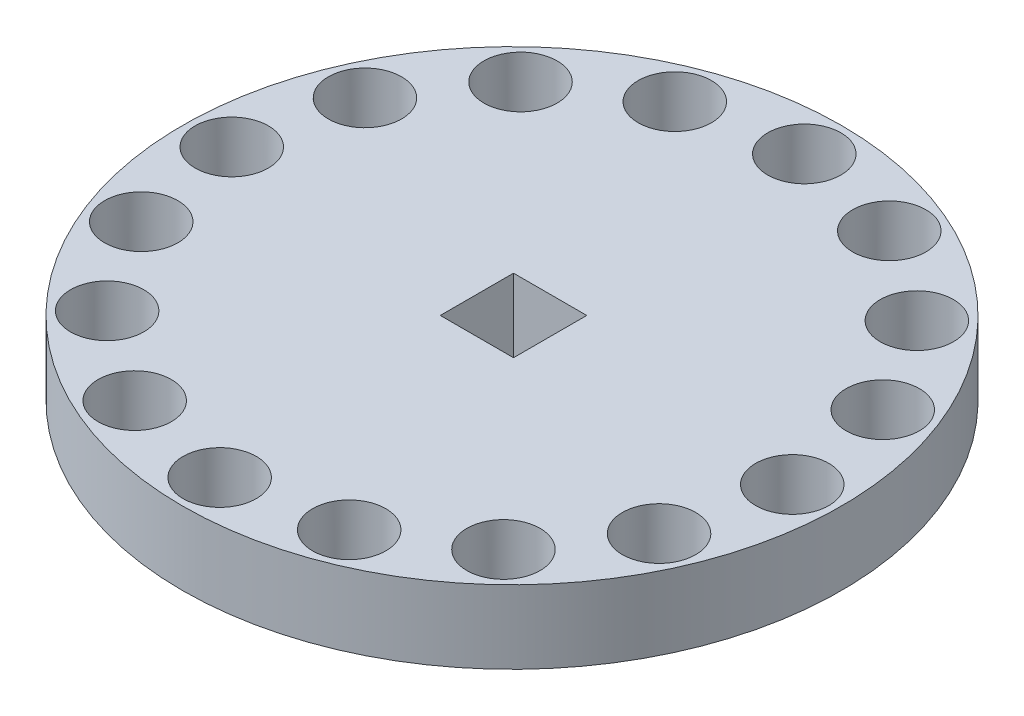
SolidWorks part; units mm, degrees
ref_plane "Ebene vorne" through (0, 0, 0) normal (0, 0, 1) x (1, 0, 0)
ref_plane "Ebene oben" through (0, 0, 0) normal (0, 1, 0) x (1, 0, 0)
ref_plane "Ebene rechts" through (0, 0, 0) normal (1, 0, 0) x (0, 0, -1)
sketch "Skizze1" plane through (0, 0, 0) normal (0, 1, 0) x (1, 0, 0)
  circle A0 centre (0, 0) radius 9
extrude "Aufsatz-Linear austragen1" add sketch "Skizze1" along normal blind 2
sketch "Skizze3" plane through (0, 2, 0) normal (0, 1, 0) x (1, 0, 0)
  line L0 (1.0142, 1.0274) -> (-0.9858, 1.0274)
  line L1 (1.0142, 1.0274) -> (1.0142, -0.9726)
  line L2 (1.0142, -0.9726) -> (-0.9858, -0.9726)
  line L3 (-0.9858, 1.0274) -> (-0.9858, -0.9726)
extrude "Schnitt-Linear austragen1" cut sketch "Skizze3" against normal blind 3
sketch "Skizze4" plane through (0, 2, 0) normal (0, 1, 0) x (1, 0, 0)
  circle A0 centre (7.818, -0.1647) radius 1
extrude "Schnitt-Linear austragen2" cut sketch "Skizze4" against normal blind 3
pattern_circular "Kreismuster1" count 16 over 360 about axis through (0, 0, 0) along (0, 1, 0) of "Schnitt-Linear austragen2"
